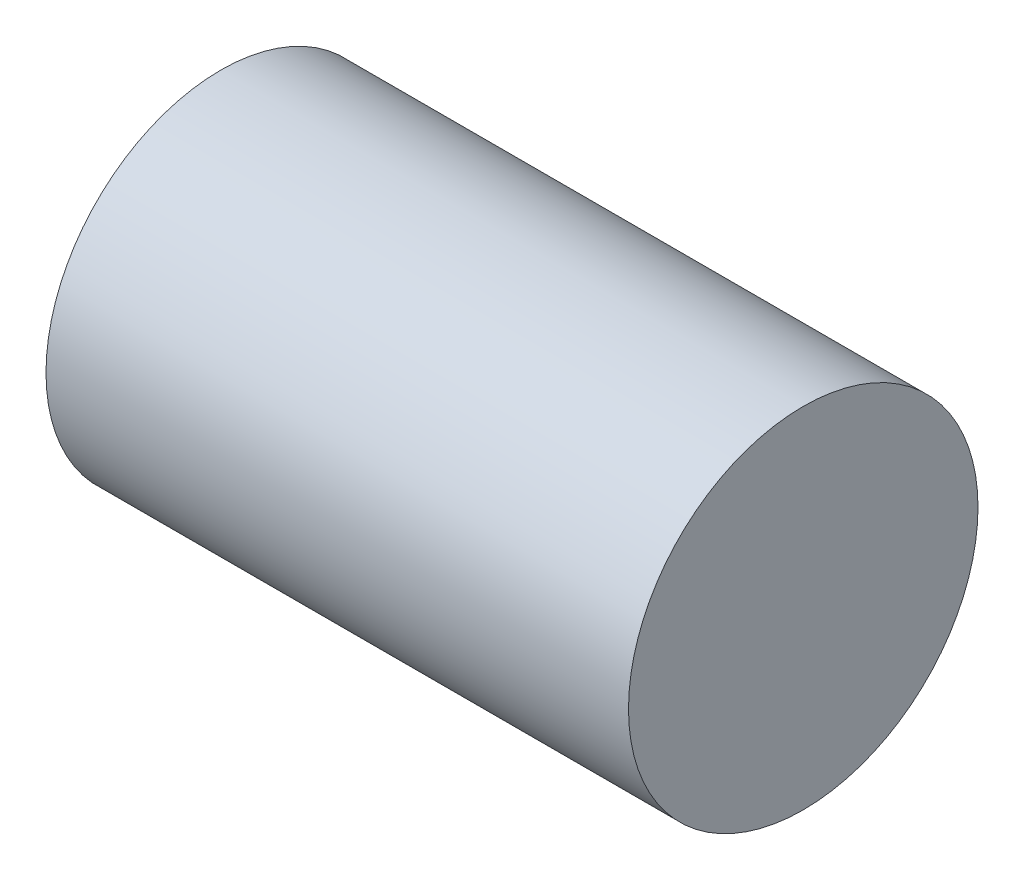
SolidWorks part; units mm, degrees
ref_plane "Plane1" through (0, 0, 0) normal (0, 0, 1) x (1, 0, 0)
ref_plane "Plane2" through (0, 0, 0) normal (0, 1, 0) x (1, 0, 0)
ref_plane "Plane3" through (0, 0, 0) normal (1, 0, 0) x (0, 0, -1)
sketch "Sketch1" plane through (0, 0, 0) normal (0, 0, 1) x (1, 0, 0)
  line L0 (-28, 0) -> (58, 0) construction
  line L1 (0, 4) -> (0, 6)
  line L2 (0, 6) -> (20, 6)
  line L3 (20, 6) -> (20, 0)
  line L4 (20, 0) -> (17, 0)
  line L5 (17, 0) -> (17, 4)
  line L6 (17, 4) -> (0, 4)
  dimension "Gevind" = 8
  dimension "Udv. dia." = 12
  dimension "Gev. længde" = 17
  dimension "Længde" = 20
revolve "Base-Revolve" add sketch "Sketch1" angle 360 about L0
sketch "Sketch2" plane through (0, 0, 0) normal (0, 0, 1) x (1, 0, 0)
  line L0 (-2, 0) -> (21, 0) construction
  line L1 (-28, 0) -> (58, 0) construction
  line L2 (20, -6) -> (20, 6) construction
  line L3 (20, 0) -> (20, 6)
  line L4 (20, 6) -> (23.5, 1.5)
  line L6 (23.5, 0) -> (20, 0)
  line L7 (23.5, 1.5) -> (23.5, 0)
  line L8 (0, 6) -> (0, -6) construction
  dimension "D1" = 23.5
  dimension "D2" = 3
revolve "Boss-Revolve1" [suppressed] add sketch "Sketch2" angle 360 about L0
fillet "Fillet2" [suppressed] radius 0.5
sketch "Sketch3" [suppressed] plane through (0, 0, 0) normal (-1, 0, 0) x (0, 0, 1)
  circle A0 centre (0, 0) radius 2.5
  circle A1 centre (0, 0) radius 2.5 construction
extrude "Cut-Extrude1" [suppressed] cut sketch "Sketch3" against normal through all
sketch "Sketch4" plane through (0, 0, 0) normal (0, 0, 1) x (1, 0, 0)
  line L0 (0, -0.4837) -> (2.5603, -0.4837)
  line L1 (0, 6) -> (0, -6) construction
  line L2 (2.5603, -0.4837) -> (2.5603, 0.4157)
  line L3 (2.5603, 0.4157) -> (0, 0.4157)
  line L4 (0, 0.4157) -> (0, -0.4837)
  dimension "D1" = 0.4157
  dimension "D2" = 0.4837
  dimension "D3" = 2.5603
extrude "Cut-Extrude2" [suppressed] cut sketch "Sketch4" against normal mid plane 19
